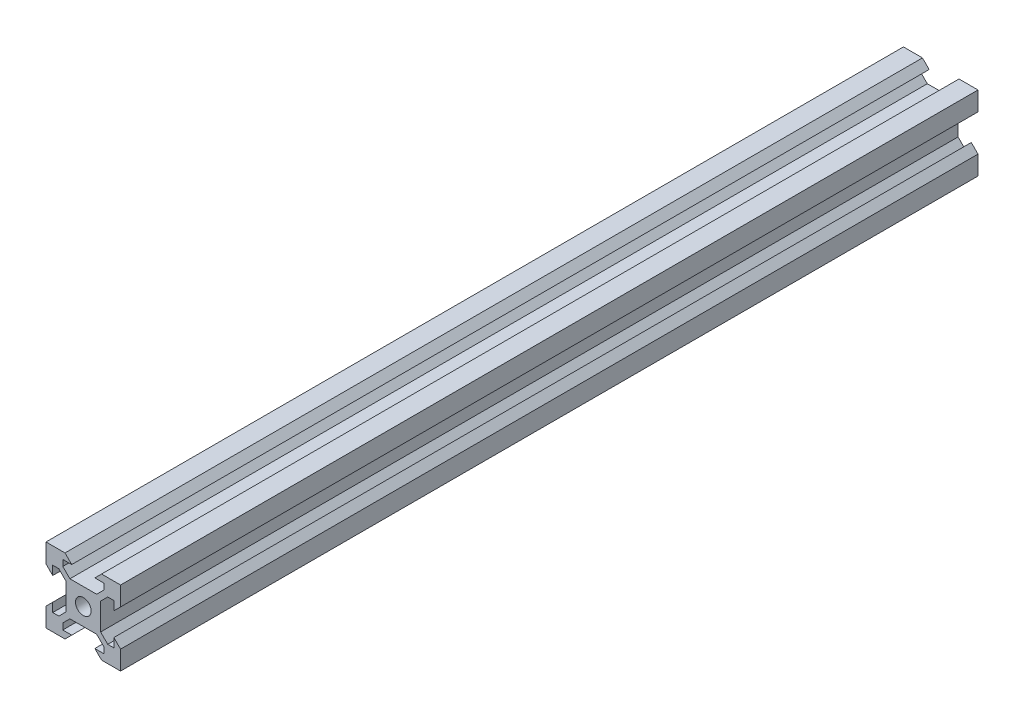
SolidWorks part; units mm, degrees
material "6063-T5"
ref_plane "Front Plane" through (0, 0, 0) normal (0, 0, 1) x (1, 0, 0)
ref_plane "Top Plane" through (0, 0, 0) normal (0, 1, 0) x (1, 0, 0)
ref_plane "Right Plane" through (0, 0, 0) normal (1, 0, 0) x (0, 0, -1)
sketch "Sketch1" plane through (0, 0, 0) normal (0, 0, 1) x (1, 0, 0)
  line L0 (3.59, 4.6507) -> (-3.59, 4.6507)
  line L5 (-10, -10) -> (10, -10)
  line L6 (-10, -10) -> (-10, 10)
  line L7 (-10, 10) -> (10, 10)
  line L8 (10, -10) -> (10, 10)
  line L9 (-10, -10) -> (10, 10) construction
  line L10 (-10, 10) -> (10, -10) construction
  line L11 (0, 10) -> (0, -10) construction
  line L12 (10, 0) -> (-10, 0) construction
  line L13 (-3.59, 4.6507) -> (-5.4993, 6.56)
  line L14 (-5.4993, 6.56) -> (-5.4993, 8.2)
  line L15 (3.59, 4.6507) -> (5.4993, 6.56)
  line L16 (5.4993, 6.56) -> (5.4993, 8.2)
  line L17 (5.4993, 8.2) -> (3.1, 8.2)
  line L18 (3.1, 8.2) -> (4.9, 10)
  line L19 (-5.4993, 8.2) -> (-3.1, 8.2)
  line L20 (-3.1, 8.2) -> (-4.9, 10)
  line L21 (3.1, -8.2) -> (4.9, -10)
  line L22 (5.4993, -8.2) -> (3.1, -8.2)
  line L23 (5.4993, -6.56) -> (5.4993, -8.2)
  line L24 (3.59, -4.6507) -> (5.4993, -6.56)
  line L25 (3.59, -4.6507) -> (-3.59, -4.6507)
  line L26 (-3.59, -4.6507) -> (-5.4993, -6.56)
  line L27 (-5.4993, -6.56) -> (-5.4993, -8.2)
  line L28 (-5.4993, -8.2) -> (-3.1, -8.2)
  line L29 (-3.1, -8.2) -> (-4.9, -10)
  line L30 (8.2, 3.1) -> (10, 4.9)
  line L31 (8.2, 3.1) -> (8.2, 5.4993)
  line L32 (8.2, 5.4993) -> (6.56, 5.4993)
  line L33 (4.6507, 3.59) -> (6.56, 5.4993)
  line L34 (4.6507, 3.59) -> (4.6507, -3.59)
  line L35 (4.6507, -3.59) -> (6.56, -5.4993)
  line L36 (8.2, -5.4993) -> (6.56, -5.4993)
  line L37 (8.2, -3.1) -> (8.2, -5.4993)
  line L38 (8.2, -3.1) -> (10, -4.9)
  line L39 (-8.2, -3.1) -> (-10, -4.9)
  line L40 (-8.2, -3.1) -> (-8.2, -5.4993)
  line L41 (-8.2, -5.4993) -> (-6.56, -5.4993)
  line L42 (-4.6507, -3.59) -> (-6.56, -5.4993)
  line L43 (-4.6507, 3.59) -> (-4.6507, -3.59)
  line L44 (-4.6507, 3.59) -> (-6.56, 5.4993)
  line L45 (-8.2, 5.4993) -> (-6.56, 5.4993)
  line L46 (-8.2, 3.1) -> (-8.2, 5.4993)
  line L47 (-8.2, 3.1) -> (-10, 4.9)
  line L48 (4.9, 10) -> (-4.9, 10)
  line L49 (-10, 4.9) -> (-10, -4.9)
  line L50 (10, -4.9) -> (10, 4.9)
  line L51 (4.9, -10) -> (-4.9, -10)
  circle A1 centre (0, 0) radius 2.1
  point P11 (0, 4.6507)
  point P35 (4.6507, 0)
  dimension "D1" = 4.2
  dimension "D2" = 20
  dimension "D3" = 20
  dimension "D4" = 0.75
  dimension "D5" = 3.59
  dimension "D6" = 3.1
  dimension "D7" = 1.8
  dimension "D8" = 1.64
  dimension "D9" = 3.59
  dimension "D10" = 1.64
  dimension "D11" = 1.8
  dimension "D12" = 45
  dimension "D13" = 0.75
  dimension "D14" = 3.1
extrude "Boss-Extrude1" add sketch "Sketch1" along normal mid plane 230 contours L6 L5 L8 L7 | A1 | L50 L30 L31 L32 L33 L34 L35 L36 L37 L38 | L48 L20 L19 L14 L13 L0 L15 L16 L17 L18 | L49 L39 L40 L41 L42 L43 L44 L45 L46 L47 | L51 L29 L28 L27 L26 L25 L24 L23 L22 L21
